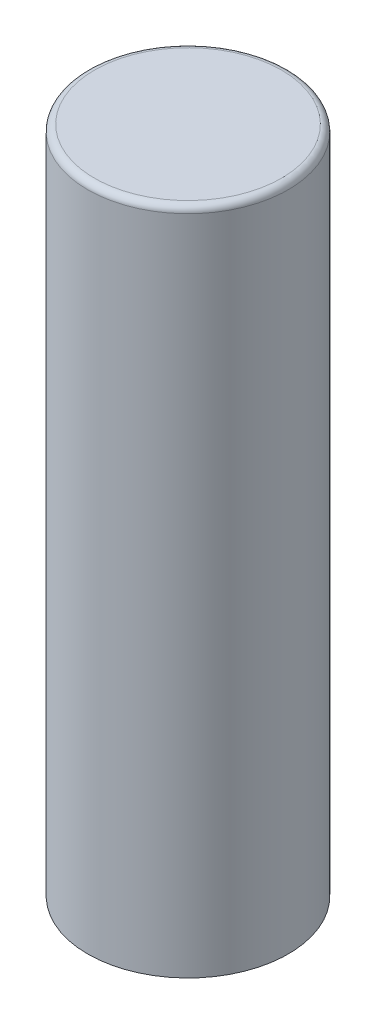
SolidWorks part; units mm, degrees
material "Bronce de aluminio"
ref_plane "Alzado" through (0, 0, 0) normal (0, 0, 1) x (1, 0, 0)
ref_plane "Planta" through (0, 0, 0) normal (0, 1, 0) x (1, 0, 0)
ref_plane "Vista lateral" through (0, 0, 0) normal (1, 0, 0) x (0, 0, -1)
sketch "Croquis1" plane through (0, 0, 0) normal (0, 0, 1) x (1, 0, 0)
  line L0 (0, 0) -> (0, 350) construction
  line L1 (0, 350) -> (-49, 350)
  line L2 (-52.5, 346.5) -> (-52.5, 0)
  line L3 (-52.5, 0) -> (-45.5, 0)
  line L4 (-45.5, 0) -> (-45.5, 343)
  line L5 (-45.5, 343) -> (0, 343)
  line L6 (0, 343) -> (0, 350)
  arc A0 (-49, 350) -> (-52.5, 346.5) centre (-49, 346.5) ccw
  dimension "D5" = 7
  dimension "D1" = 350
  dimension "D2" = 45.5
  dimension "D3" = 7
  dimension "D4" = 7
revolve "Revolución1" add sketch "Croquis1" angle 360 about L0
